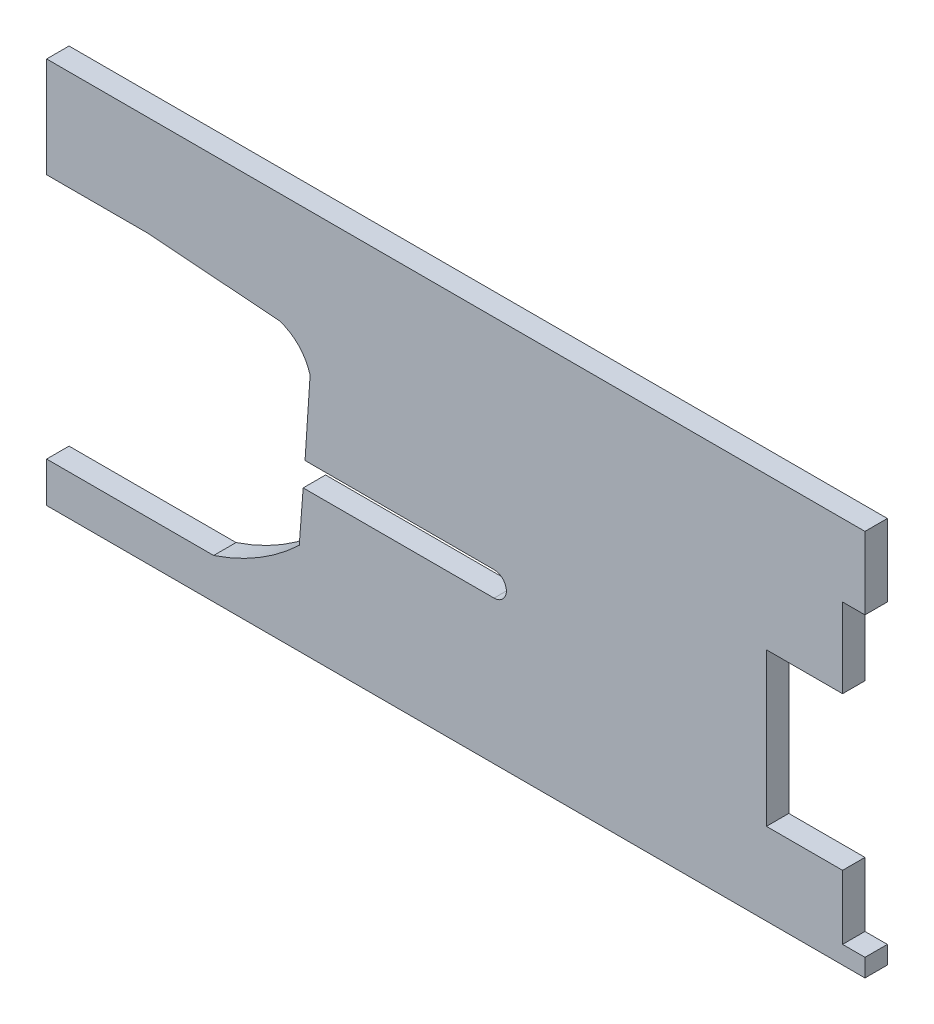
SolidWorks part; units mm, degrees
ref_plane "Front" through (0, 0, 0) normal (0, 0, 1) x (1, 0, 0)
ref_plane "Top" through (0, 0, 0) normal (0, 1, 0) x (1, 0, 0)
ref_plane "Right" through (0, 0, 0) normal (1, 0, 0) x (0, 0, -1)
sketch "Sketch1" plane through (0, 0, 0) normal (0, 0, 1) x (1, 0, 0)
  line L1 (-122.5339, 0) -> (0, 0)
  line L2 (-182.7, 63.949) -> (-182.7, 86.3509)
  line L3 (-182.7, 86.3509) -> (0, 86.3509)
  line L4 (0, 0) -> (0, 4)
  line L5 (-160.2568, 63.949) -> (-130.7245, 61.7095)
  line L6 (-172.7, 90.9941) -> (10, 90.9941) construction
  line L7 (-125.428, 32.0484) -> (-82.8102, 32.0484)
  line L8 (-125.428, 32.0484) -> (-126.3018, 20.511)
  line L9 (-125.0114, 37.5484) -> (-82.8102, 37.5484)
  line L10 (-122.5339, 0) -> (-182.7, 0)
  line L12 (-145.4106, 8.9918) -> (-182.7, 8.9918)
  line L13 (-182.7, 0) -> (-182.7, 8.9918)
  line L14 (-161.5736, 57.4131) -> (-124.177, 54.6294) construction
  line L15 (-182.7, 63.949) -> (-160.2568, 63.949)
  line L16 (-125.0114, 37.5484) -> (-123.8786, 54.6294)
  line L17 (-161.5736, 57.4131) -> (-164.3573, 20.0166) construction
  line L18 (-164.3573, 20.0166) -> (-126.9608, 17.2328) construction
  line L19 (-124.177, 54.6294) -> (-126.9608, 17.2328) construction
  line L20 (-22, 52.4636) -> (-5, 52.4636)
  line L22 (-5, 18.3222) -> (-22, 18.3222)
  line L26 (0, 70.203) -> (0, 86.3509)
  line L45 (-22, 52.4636) -> (-22, 18.3222)
  line L46 (0, 70.203) -> (-5, 70.203)
  line L48 (0, 4) -> (-5, 4)
  line L49 (-5, 70.203) -> (-5, 52.4636)
  line L53 (-5, 18.3222) -> (-5, 13.9026)
  line L54 (-5, 8.9026) -> (-5, 4)
  line L55 (-5, 13.9026) -> (-23, 13.9026) construction
  line L56 (-5, 13.9026) -> (-5, 8.9026)
  line L57 (-5, 8.9026) -> (-23, 8.9026) construction
  line L58 (-23, 13.9026) -> (-23, 8.9026) construction
  arc A0 (-123.8786, 54.6294) -> (-130.7245, 61.7095) centre (-133.8182, 51.8684) ccw
  arc A1 (-82.8102, 32.0484) -> (-82.8102, 37.5484) centre (-82.8102, 34.7984) ccw
  circle A2 centre (-133.3359, 24.6334) radius 6.9069 construction
  arc A3 (-145.4106, 8.9918) -> (-126.3018, 20.511) centre (-161.5736, 57.4131) ccw
  point P0 (0, 0)
  dimension "D1" = 5.5
  dimension "D2" = 37.5
  dimension "D3" = 22
  dimension "D4" = 18
extrude "Boss-Extrude1" add sketch "Sketch1" along normal blind 5
